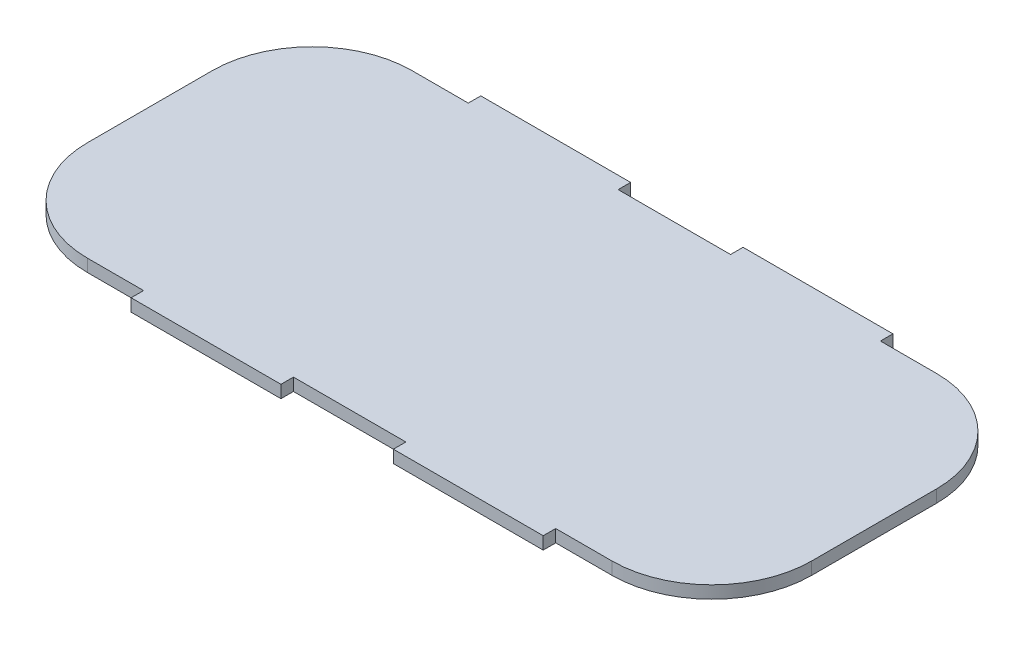
SolidWorks part; units mm, degrees
ref_plane "Front Plane" through (0, 0, 0) normal (0, 0, 1) x (1, 0, 0)
ref_plane "Top Plane" through (0, 0, 0) normal (0, 1, 0) x (1, 0, 0)
ref_plane "Right Plane" through (0, 0, 0) normal (1, 0, 0) x (0, 0, -1)
sketch "Sketch1" plane through (0, 0, 0) normal (0, 1, 0) x (1, 0, 0)
  line L0 (0, 83.3808) -> (0, -83.3808) construction
  line L1 (-52.5, 32.5) -> (-41.25, 32.5)
  line L2 (-72.5, 12.5) -> (-72.5, -12.5)
  line L3 (-52.5, -32.5) -> (-41.25, -32.5)
  line L4 (72.5, 12.5) -> (72.5, -12.5)
  line L5 (-72.5, 32.5) -> (72.5, -32.5) construction
  line L6 (-72.5, -32.5) -> (72.5, 32.5) construction
  line L7 (136.9216, 0) -> (-136.9216, 0) construction
  line L11 (-41.25, 35) -> (-11.25, 35)
  line L12 (-41.25, 35) -> (-41.25, 32.5)
  line L14 (-11.25, 35) -> (-11.25, 32.5)
  line L15 (41.25, 32.5) -> (52.5, 32.5)
  line L16 (-11.25, -32.5) -> (11.25, -32.5)
  line L17 (-11.25, -35) -> (-11.25, -32.5)
  line L18 (-41.25, -35) -> (-11.25, -35)
  line L19 (-41.25, -35) -> (-41.25, -32.5)
  line L20 (41.25, -35) -> (41.25, -32.5)
  line L21 (41.25, -35) -> (11.25, -35)
  line L22 (11.25, -35) -> (11.25, -32.5)
  line L25 (11.25, 35) -> (11.25, 32.5)
  line L26 (41.25, 35) -> (11.25, 35)
  line L27 (41.25, 35) -> (41.25, 32.5)
  line L28 (-11.25, 32.5) -> (11.25, 32.5)
  line L31 (41.25, -32.5) -> (52.5, -32.5)
  arc A0 (52.5, 32.5) -> (72.5, 12.5) centre (52.5, 12.5) cw
  arc A1 (72.5, -12.5) -> (52.5, -32.5) centre (52.5, -12.5) cw
  arc A2 (-52.5, -32.5) -> (-72.5, -12.5) centre (-52.5, -12.5) cw
  arc A3 (-72.5, 12.5) -> (-52.5, 32.5) centre (-52.5, 12.5) cw
  point P0 (0, 0)
  point P18 (-26.25, 32.5)
  point P21 (0, 0)
  point P24 (0, 0)
  dimension "D3" = 20
  dimension "D1" = 145
  dimension "D2" = 65
extrude "Boss-Extrude2" add sketch "Sketch1" along normal blind 2.5
